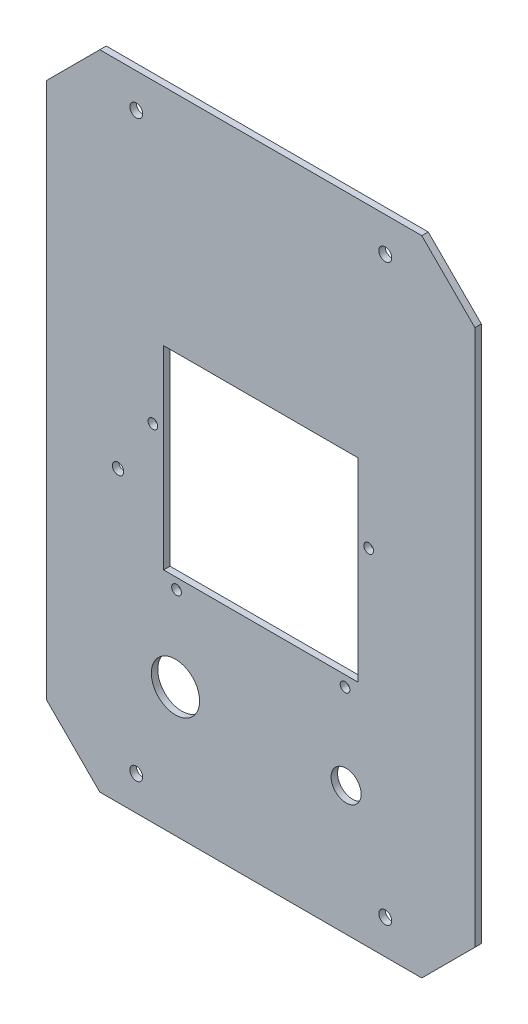
SolidWorks part; units mm, degrees
material "Alliage 1060"
ref_plane "Plan de dessus" through (0, 0, 0) normal (0, 0, 1) x (1, 0, 0)
ref_plane "Plan de droite" through (0, 0, 0) normal (0, 1, 0) x (1, 0, 0)
ref_plane "Plan de face" through (0, 0, 0) normal (1, 0, 0) x (0, 0, -1)
sketch "Esquisse1" plane through (0, 0, 0) normal (0, 0, 1) x (1, 0, 0)
  line L0 (0, 0) -> (-150, 0)
  line L1 (-150, 0) -> (-174.7487, 24.7487)
  line L2 (-174.7487, 24.7487) -> (-174.7487, 274.7487)
  line L3 (-174.7487, 274.7487) -> (-150, 299.4975)
  line L4 (-150, 299.4975) -> (0, 299.4975)
  line L5 (0, 299.4975) -> (24.7487, 274.7487)
  line L6 (24.7487, 274.7487) -> (24.7487, 24.7487)
  line L7 (24.7487, 24.7487) -> (0, 0)
  line L9 (-150, 299.4975) -> (0, 299.4975)
  line L10 (-174.7487, 274.7487) -> (-174.7487, 24.7487)
  line L12 (24.7487, 274.7487) -> (24.7487, 24.7487)
  dimension "D1" = 250
  dimension "D2" = 35
  dimension "D3" = 135
  dimension "D4" = 150
extrude "Base" add sketch "Esquisse1" along normal blind 3 contours L7 L6 L5 L4 L3 L2 L1 L0
sketch "Esquisse2" plane through (0, 0, 0) normal (0, 0, -1) x (-1, 0, 0)
  line L0 (75, 299.4975) -> (75, 0) construction
  line L1 (150, 299.4975) -> (0, 299.4975) construction
  line L2 (0, 0) -> (150, 0) construction
  line L3 (174.7487, 149.7487) -> (-24.7487, 149.7487) construction
  line L4 (174.7487, 24.7487) -> (174.7487, 274.7487) construction
  line L5 (-24.7487, 274.7487) -> (-24.7487, 24.7487) construction
  circle A0 centre (132.9987, 283.4975) radius 3
  circle A1 centre (132.9987, 16) radius 3
  circle A2 centre (17.0013, 16) radius 3
  circle A3 centre (17.0013, 283.4975) radius 3
  dimension "D1" = 6
  dimension "D2" = 41.75
  dimension "D3" = 16
extrude "Enlèv. mat.-Extru.1" cut sketch "Esquisse2" against normal through all
sketch "Esquisse3" plane through (0, 0, 0) normal (0, 0, -1) x (-1, 0, 0)
  line L1 (0, 0) -> (150, 0) construction
  line L2 (174.7487, 24.7487) -> (174.7487, 274.7487) construction
  line L3 (-24.7487, 274.7487) -> (-24.7487, 24.7487) construction
  circle A0 centre (114.7487, 60) radius 11.25
  circle A1 centre (35.2513, 60) radius 7
  dimension "D1" = 22.5
  dimension "D4" = 14
  dimension "D6" = 60
  dimension "D2" = 60
  dimension "D3" = 60
  dimension "D5" = 60
extrude "Enlèv. mat.-Extru.2" cut sketch "Esquisse3" against normal up to next
sketch "Esquisse4" plane through (0, 0, 0) normal (0, 0, -1) x (-1, 0, 0)
  line L1 (0, 0) -> (150, 0) construction
  line L2 (174.7487, 24.7487) -> (174.7487, 274.7487) construction
  circle A0 centre (141.4987, 134.75) radius 2.625
  dimension "D1" = 5.25
  dimension "D2" = 33.25
  dimension "D3" = 134.75
extrude "Enlèv. mat.-Extru.3" cut sketch "Esquisse4" against normal up to next
sketch "Esquisse5" plane through (0, 0, 3) normal (0, 0, 1) x (1, 0, 0)
  line L0 (-150, 299.4975) -> (0, 299.4975) construction
  line L1 (-120.25, 194.9987) -> (-29.75, 194.9987)
  line L2 (-120.25, 194.9987) -> (-120.25, 104.4987)
  line L3 (-120.25, 104.4987) -> (-29.75, 104.4987)
  line L4 (-29.75, 194.9987) -> (-29.75, 104.4987)
  line L5 (24.7487, 274.7487) -> (24.7487, 24.7487) construction
  point P6 (-75, 299.4975)
  point P7 (-75, 194.9987)
  point P10 (24.7487, 149.7487)
  point P11 (-29.75, 149.7487)
  dimension "D1" = 90.5
  dimension "D2" = 90.5
extrude "Enlèv. mat.-Extru.4" cut sketch "Esquisse5" against normal up to next
sketch "Esquisse6" plane through (0, 0, 0) normal (0, 0, -1) x (-1, 0, 0)
  line L0 (29.75, 194.9987) -> (29.75, 104.4987) construction
  line L1 (120.25, 194.9987) -> (29.75, 194.9987) construction
  line L2 (29.75, 104.4987) -> (120.25, 104.4987) construction
  line L3 (120.25, 104.4987) -> (120.25, 194.9987) construction
  circle A1 centre (125.25, 160.9987) radius 2.25
  circle A3 centre (35.75, 99.4987) radius 2.25
  circle A4 centre (114.25, 99.4987) radius 2.25
  circle A5 centre (24.75, 160.9987) radius 2.25
  dimension "D1" = 4.5
  dimension "D2" = 4.5
  dimension "D4" = 4.5
  dimension "D13" = 4.5
  dimension "D5" = 34
  dimension "D6" = 5
  dimension "D9" = 6
  dimension "D10" = 5
  dimension "D11" = 6
  dimension "D12" = 5
  dimension "D14" = 5
  dimension "D15" = 34
extrude "Enlèv. mat.-Extru.5" cut sketch "Esquisse6" against normal blind 10
